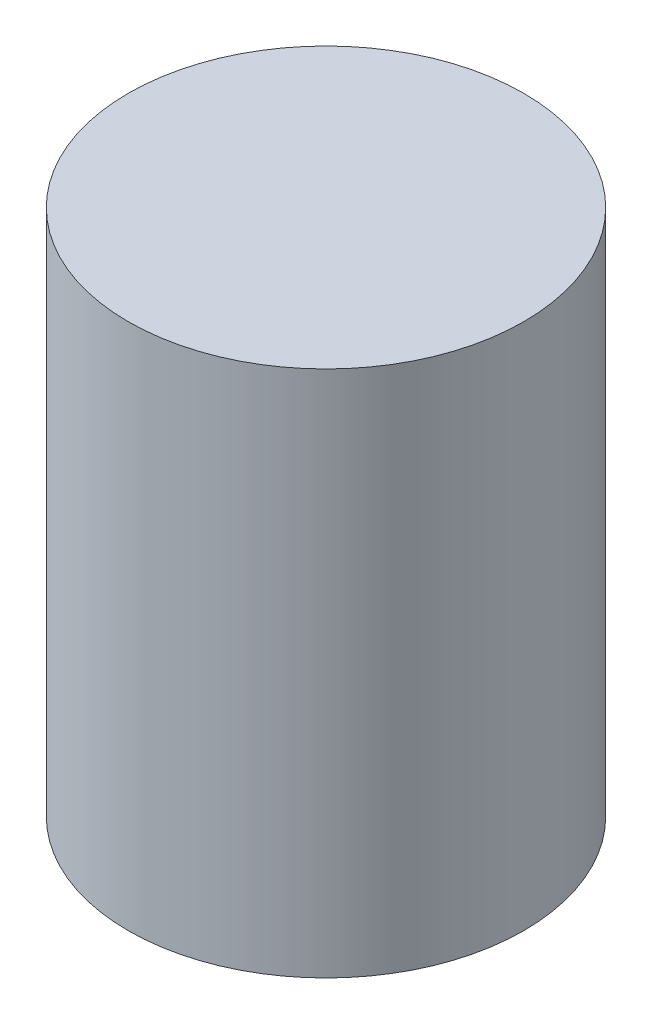
SolidWorks part; units mm, degrees
material "Brass"
ref_plane "Front Plane" through (0, 0, 0) normal (0, 0, 1) x (1, 0, 0)
ref_plane "Top Plane" through (0, 0, 0) normal (0, 1, 0) x (1, 0, 0)
ref_plane "Right Plane" through (0, 0, 0) normal (1, 0, 0) x (0, 0, -1)
other "Center of Mass"
sketch "Sketch1" plane through (0, 0, 0) normal (0, 1, 0) x (1, 0, 0)
  circle A0 centre (0, 0) radius 28.575
  dimension "D1" = 57.15
extrude "Boss-Extrude1" add sketch "Sketch1" along normal blind 76.2
hole_wizard "1/2-13 Tapped Hole1" positions "Sketch2" profile "Sketch3" tap size "1/2-13" standard "ANSI Inch"
sketch "Sketch2" plane through (0, 0, 0) normal (0, 1, 0) x (1, 0, 0)
  point P0 (0, 0)
sketch "Sketch3" plane through (0, 0, 0) normal (1, 0, 0) x (0, 0, -1)
  line L0 (0, 0) -> (0, 43.2195)
  line L1 (0, 43.2195) -> (5.3581, 40)
  line L2 (5.3581, 40) -> (5.3581, 0)
  line L5 (5.3581, 0) -> (0, 0)
  line L10 (0, 43.2195) -> (-5.3581, 40) construction
  line L11 (0, -6.35) -> (0, 107.95) construction
  dimension "Tap Drill Dia." = 10.7163
  dimension "Tap Drill Depth" = 40
  dimension "Drill Angle" = 118
